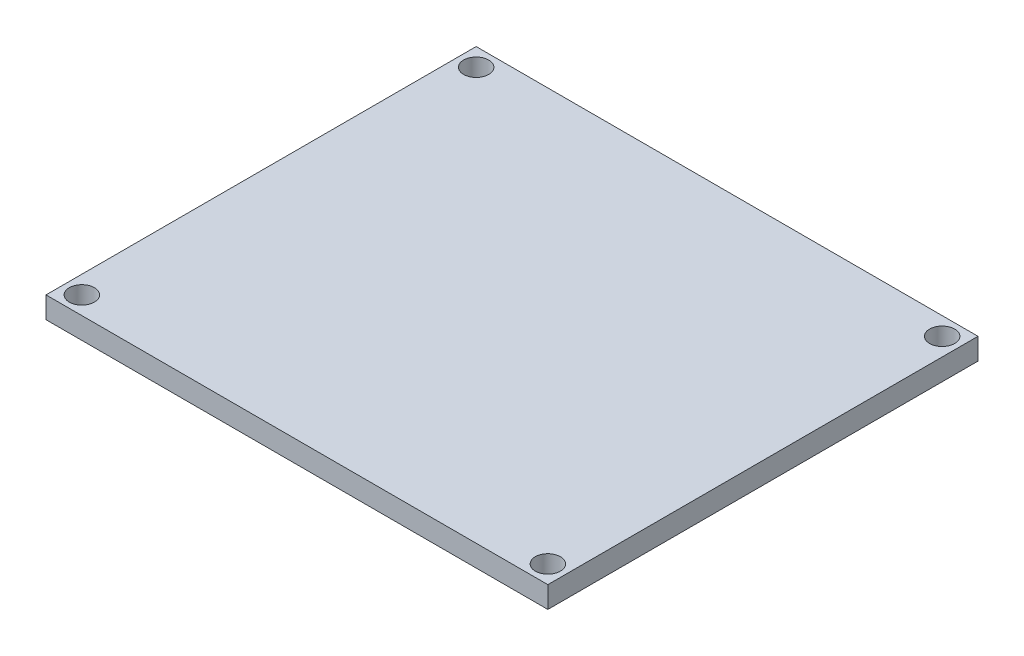
SolidWorks part; units mm, degrees
ref_plane "Front Plane" through (0, 0, 0) normal (0, 0, 1) x (1, 0, 0)
ref_plane "Top Plane" through (0, 0, 0) normal (0, 1, 0) x (1, 0, 0)
ref_plane "Right Plane" through (0, 0, 0) normal (1, 0, 0) x (0, 0, -1)
sketch "Sketch1" plane through (0, 0, 0) normal (0, 1, 0) x (1, 0, 0)
  line L1 (-30.9375, -11.4062) -> (39.0625, -11.4062)
  line L2 (-30.9375, -11.4062) -> (-30.9375, 48.5938)
  line L3 (-30.9375, 48.5938) -> (39.0625, 48.5938)
  line L4 (39.0625, -11.4062) -> (39.0625, 48.5938)
  dimension "D1" = 70
  dimension "D2" = 60
extrude "Boss-Extrude1" add sketch "Sketch1" along normal blind 3
sketch "Sketch2" plane through (0, 3, 0) normal (0, 1, 0) x (1, 0, 0)
  line L0 (-30.9375, 48.5938) -> (-30.9375, -11.4062) construction
  line L1 (39.0625, 48.5938) -> (-30.9375, 48.5938) construction
  line L2 (39.0625, -11.4062) -> (39.0625, 48.5938) construction
  line L3 (-30.9375, -11.4062) -> (39.0625, -11.4062) construction
  circle A0 centre (-28.4375, 46.0938) radius 1.75
  circle A1 centre (36.5625, 46.0938) radius 1.75
  circle A2 centre (36.5625, -8.9062) radius 1.75
  circle A3 centre (-28.4375, -8.9062) radius 1.75
  dimension "D1" = 3.5
  dimension "D2" = 3.5
  dimension "D3" = 3.5
  dimension "D4" = 3.5
  dimension "D5" = 2.5
  dimension "D6" = 2.5
  dimension "D7" = 2.5
  dimension "D8" = 2.5
  dimension "D9" = 2.5
  dimension "D10" = 2.5
  dimension "D11" = 2.5
  dimension "D12" = 2.5
extrude "Cut-Extrude1" cut sketch "Sketch2" against normal blind 6
